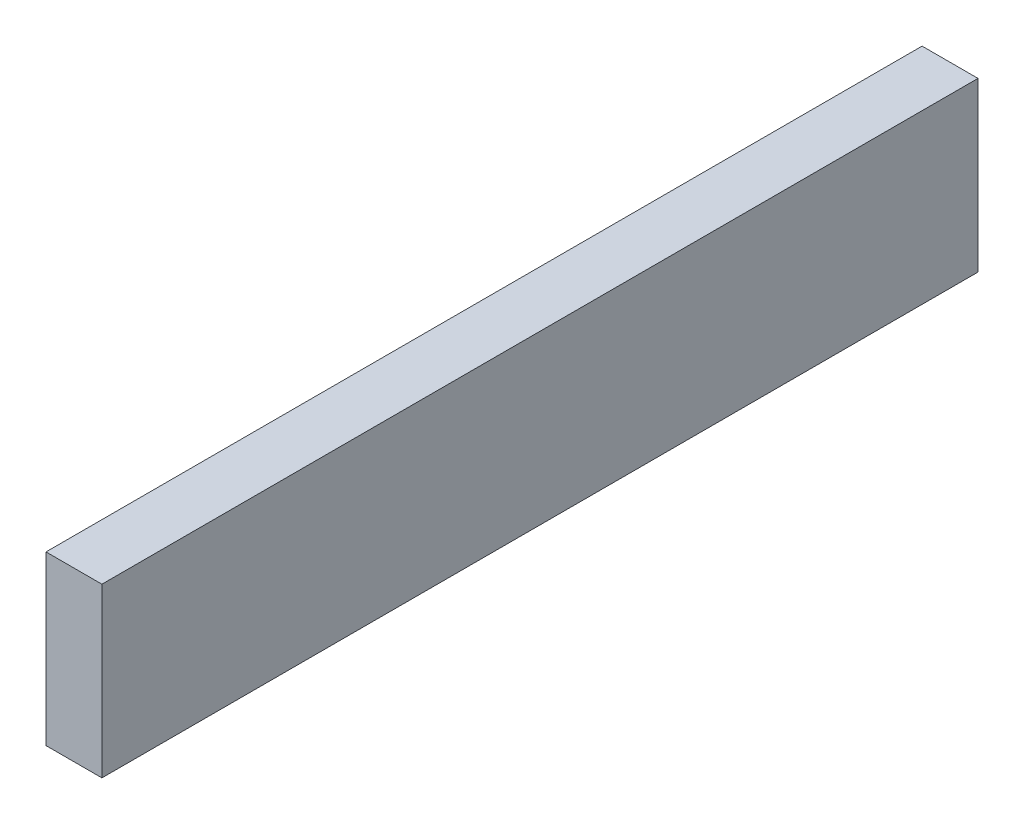
SolidWorks part; units mm, degrees
ref_plane "Front Plane" through (0, 0, 0) normal (0, 0, 1) x (1, 0, 0)
ref_plane "Top Plane" through (0, 0, 0) normal (0, 1, 0) x (1, 0, 0)
ref_plane "Right Plane" through (0, 0, 0) normal (1, 0, 0) x (0, 0, -1)
sketch "Sketch1" plane through (0, 0, 0) normal (0, 0, 1) x (1, 0, 0)
  line L1 (-15, -45) -> (15, -45)
  line L2 (-15, -45) -> (-15, 45)
  line L3 (-15, 45) -> (15, 45)
  line L4 (15, -45) -> (15, 45)
  line L5 (-15, -45) -> (15, 45) construction
  line L6 (-15, 45) -> (15, -45) construction
  point P0 (0, 0)
  dimension "D1" = 30
  dimension "D2" = 90
extrude "Boss-Extrude1" add sketch "Sketch1" along normal mid plane 470
